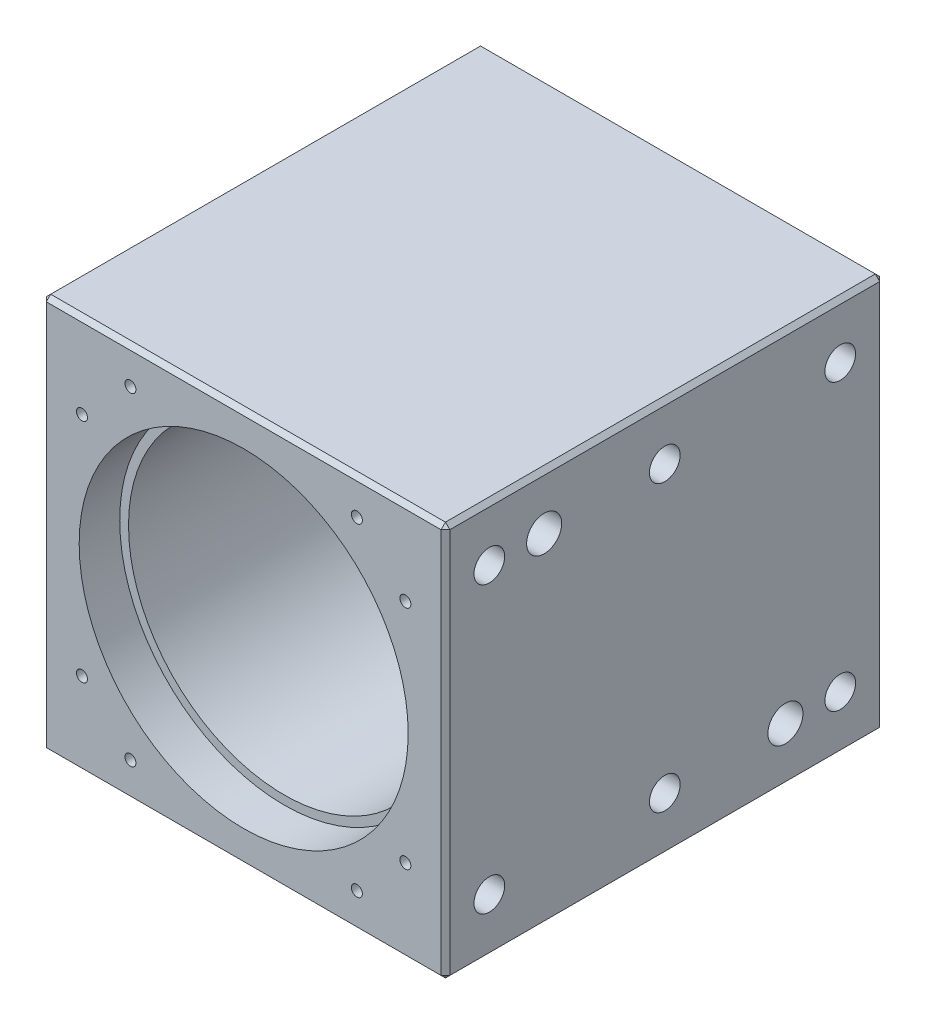
SolidWorks part; units mm, degrees
material "S235JR  (1.0037  ST37)"
ref_plane "Ebene vorne" through (0, 0, 0) normal (0, 0, 1) x (1, 0, 0)
ref_plane "Ebene oben" through (0, 0, 0) normal (0, 1, 0) x (1, 0, 0)
ref_plane "Ebene rechts" through (0, 0, 0) normal (1, 0, 0) x (0, 0, -1)
sketch "Skizze1" plane through (0, 0, 0) normal (0, 0, 1) x (1, 0, 0)
  line L0 (-92, -90) -> (92, -90)
  line L1 (92, -90) -> (92, 90)
  line L2 (92, 90) -> (-92, 90)
  line L3 (-92, 90) -> (-92, -90)
  point P4 (0, 90)
  point P6 (-92, 0)
extrude "Extrusion1" add sketch "Skizze1" along normal blind 200
sketch "Skizze2" plane through (0, 0, 200) normal (0, 0, 1) x (1, 0, 0)
  circle A0 centre (0, 0) radius 75
  dimension "D1" = 150
extrude "Extrusion2" cut sketch "Skizze2" against normal blind 18.5
sketch "Skizze3" plane through (0, 0, 0) normal (0, 0, -1) x (-1, 0, 0)
  circle A0 centre (0, 0) radius 75
  dimension "D1" = 150
extrude "Extrusion3" cut sketch "Skizze3" against normal blind 16.5
hole_wizard "M6 Gewindebohrung1" positions "Skizze9" profile "Skizze10" tap size "M6" standard "DIN"
sketch "Skizze9" plane through (0, 0, 0) normal (0, 0, -1) x (-1, 0, 0)
  line L0 (-69.6279, 48.754) -> (0, 0) construction
  line L2 (101.2, 0) -> (-101.2, 0) construction
  line L3 (-48.754, 69.6279) -> (0, 0) construction
  circle A0 centre (0, 0) radius 85 construction
  point P0 (-69.6279, 48.754)
  point P17 (-48.754, 69.6279)
  dimension "D1" = 170
  dimension "D2" = 35
  dimension "D3" = 20
sketch "Skizze10" plane through (69.6279, 48.754, 0) normal (1, 0, 0) x (0, 1, 0)
  line L0 (0, 0) -> (0, 18.5022)
  line L1 (0, 18.5022) -> (2.5, 17)
  line L2 (2.5, 17) -> (2.5, 0)
  line L5 (2.5, 0) -> (0, 0)
  line L10 (0, 18.5022) -> (-2.5, 17) construction
  line L11 (0, -6.35) -> (0, 107.95) construction
  dimension "Bohrerdurchmesser" = 5
  dimension "Bohrungstiefe" = 17
  dimension "Spitzenwinkel" = 118
cosmetic thread "Bohrungsgewinde11" parameters "D1"=12, "D2"=6
cosmetic thread "Bohrungsgewinde17" parameters "D1"=12, "D2"=6
sketch "Skizze6" plane through (0, 0, 16.5) normal (0, 0, -1) x (-1, 0, 0)
  circle A0 centre (0, 0) radius 71
  dimension "D1" = 142
extrude "Extrusion4" cut sketch "Skizze6" against normal blind 180
chamfer "Fase1" distance 2 distance2 2 12 edges at (-92, 0, 200) (0, -90, 200) (92, 0, 200) (0, 90, 200) (-92, 90, 100) (-92, -90, 100) (92, -90, 100) (92, 90, 100) (0, 90, 0) (92, 0, 0) (-92, 0, 0) (0, -90, 0)
hole_wizard "M16 Gewindebohrung3" positions "Skizze13" profile "Skizze14" tap size "M16" standard "DIN"
sketch "Skizze13" plane through (-92, 0, 0) normal (-1, 0, 0) x (0, 0, 1)
  line L0 (200, 88) -> (200, -88) construction
  line L1 (180, 65) -> (180, -65) construction
  point P0 (180, 65)
  point P9 (180, 0)
cosmetic thread "Bohrungsgewinde10" parameters "D1"=30, "D2"=16
sketch "Skizze14" plane through (-92, 65, 180) normal (0, 1, 0) x (0, 0, 1)
  line L0 (0, 0) -> (0, 42.206)
  line L1 (0, 42.206) -> (7, 38)
  line L2 (7, 38) -> (7, 0)
  line L5 (7, 0) -> (0, 0)
  line L10 (0, 42.206) -> (-7, 38) construction
  line L11 (0, -6.35) -> (0, 107.95) construction
  dimension "Bohrerdurchmesser" = 14
  dimension "Bohrungstiefe" = 38
  dimension "Spitzenwinkel" = 118
pattern_linear "Lineares Muster111" count 3 spacing 80 along (0, 0, -1) count 2 spacing 130 along (0, -1, 0) of "M16 Gewindebohrung3"
mirror "Spiegeln3" about plane through (0, 0, 0) normal (1, 0, 0) of "Lineares Muster111", "M16 Gewindebohrung3"
pattern_circular "Kreismuster1" count 4 over 360 about axis through (0, 0, 0) along (0, 0, 1) of "M6 Gewindebohrung1"
hole_wizard "M6 Gewindebohrung2" positions "Skizze15" profile "Skizze16" tap size "M6" standard "DIN"
sketch "Skizze15" plane through (0, 0, 200) normal (0, 0, 1) x (1, 0, 0)
  line L0 (-73.7237, 51.6219) -> (0, 0) construction
  line L2 (101.2, 0) -> (-101.2, 0) construction
  line L3 (-51.6219, 73.7237) -> (0, 0) construction
  circle A0 centre (0, 0) radius 90 construction
  point P0 (-73.7237, 51.6219)
  point P13 (-51.6219, 73.7237)
  dimension "D1" = 35
  dimension "D2" = 180
  dimension "D3" = 20
cosmetic thread "Bohrungsgewinde15" parameters "D1"=12, "D2"=6
sketch "Skizze16" plane through (-73.7237, 51.6219, 200) normal (1, 0, 0) x (0, -1, 0)
  line L0 (0, 0) -> (0, 18.5022)
  line L1 (0, 18.5022) -> (2.5, 17)
  line L2 (2.5, 17) -> (2.5, 0)
  line L5 (2.5, 0) -> (0, 0)
  line L10 (0, 18.5022) -> (-2.5, 17) construction
  line L11 (0, -6.35) -> (0, 107.95) construction
  dimension "Bohrerdurchmesser" = 5
  dimension "Bohrungstiefe" = 17
  dimension "Spitzenwinkel" = 118
cosmetic thread "Bohrungsgewinde16" parameters "D1"=12, "D2"=6
pattern_circular "Kreismuster2" count 4 over 360 about axis through (0, 0, 0) along (0, 0, 1) of "M6 Gewindebohrung2"
hole_wizard "Ø16.0 (16) Durchmesser Bohrung1" positions "Skizze17" profile "Skizze18" hole size "Ø16.0" standard "DIN"
sketch "Skizze17" plane through (92, 0, 0) normal (1, 0, 0) x (0, 0, -1)
  circle A0 centre (-180, 65) radius 7 construction
  circle A1 centre (-20, -65) radius 7 construction
  point P0 (-155, 65)
  point P3 (-45, -65)
  dimension "D1" = 25
  dimension "D2" = 25
sketch "Skizze18" plane through (92, 65, 155) normal (0, 1, 0) x (0, 0, -1)
  line L0 (0, 0) -> (0, 27.0569)
  line L1 (0, 27.0569) -> (8, 22.25)
  line L2 (8, 22.25) -> (8, 0)
  line L5 (8, 0) -> (0, 0)
  line L10 (0, 27.0569) -> (-8, 22.25) construction
  line L11 (0, -6.35) -> (0, 107.95) construction
  dimension "Bohrerdurchmesser" = 16
  dimension "Bohrungstiefe" = 22.25
  dimension "Spitzenwinkel" = 118
mirror "Spiegeln4" about plane through (0, 0, 0) normal (1, 0, 0) of "Ø16.0 (16) Durchmesser Bohrung1"
hole_wizard "M5 Gewindebohrung1" positions "Skizze19" profile "Skizze20" tap size "M5" standard "DIN"
sketch "Skizze19" plane through (0, -90, 0) normal (0, -1, 0) x (-1, 0, 0)
  line L0 (90, -200) -> (-90, -200) construction
  line L1 (-92, -198) -> (-92, -2) construction
  point P0 (-40, -180)
  point P2 (-18, -180)
  dimension "D1" = 22
  dimension "D2" = 20
  dimension "D3" = 52
cosmetic thread "Bohrungsgewinde18" parameters "D1"=6, "D2"=5
cosmetic thread "Bohrungsgewinde19" parameters "D1"=6, "D2"=5
sketch "Skizze20" plane through (40, -90, 180) normal (1, 0, 0) x (0, 0, -1)
  line L0 (0, 0) -> (0, 11.2618)
  line L1 (0, 11.2618) -> (2.1, 10)
  line L2 (2.1, 10) -> (2.1, 0)
  line L5 (2.1, 0) -> (0, 0)
  line L10 (0, 11.2618) -> (-2.1, 10) construction
  line L11 (0, -6.35) -> (0, 107.95) construction
  dimension "Bohrerdurchmesser" = 4.2
  dimension "Bohrungstiefe" = 10
  dimension "Spitzenwinkel" = 118
equation "\"D4@Lineares Muster111\"=\"D2@Skizze13\""
